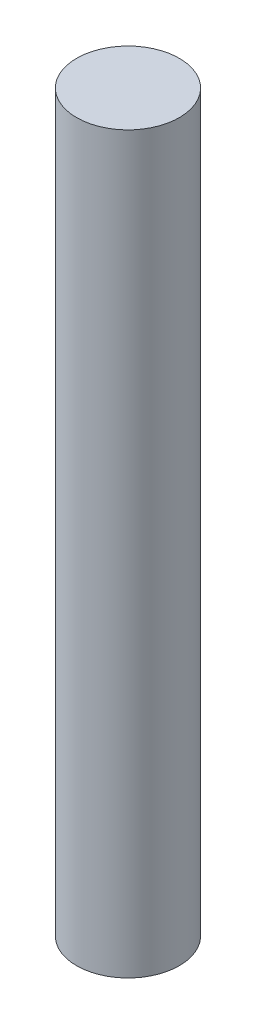
SolidWorks part; units mm, degrees
ref_plane "Front Plane" through (0, 0, 0) normal (0, 0, 1) x (1, 0, 0)
ref_plane "Top Plane" through (0, 0, 0) normal (0, 1, 0) x (1, 0, 0)
ref_plane "Right Plane" through (0, 0, 0) normal (1, 0, 0) x (0, 0, -1)
sketch "Sketch1" plane through (0, 0, 0) normal (0, 1, 0) x (1, 0, 0)
  circle A0 centre (0, 0) radius 3.175
extrude "Boss-Extrude1" add sketch "Sketch1" along normal blind 45.3898
